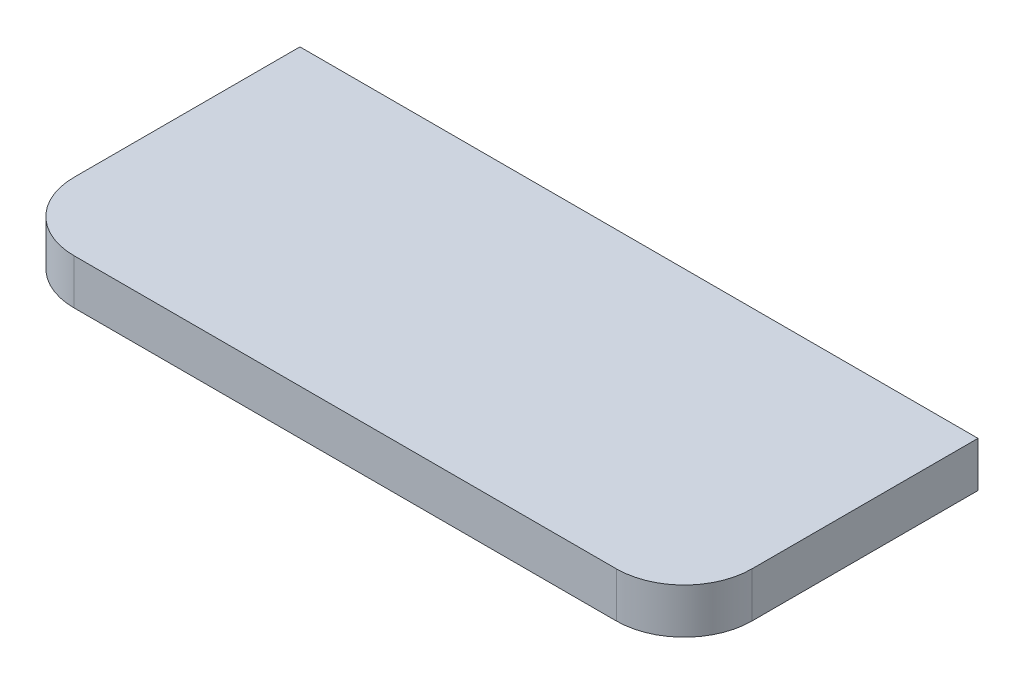
SolidWorks part; units mm, degrees
ref_plane "Front Plane" through (0, 0, 0) normal (0, 0, 1) x (1, 0, 0)
ref_plane "Top Plane" through (0, 0, 0) normal (0, 1, 0) x (1, 0, 0)
ref_plane "Right Plane" through (0, 0, 0) normal (1, 0, 0) x (0, 0, -1)
sketch "Sketch1" plane through (0, 0, 0) normal (0, 1, 0) x (1, 0, 0)
  line L0 (-75, 0) -> (75, 0)
  line L1 (75, 0) -> (75, -50)
  line L2 (-75, 0) -> (-75, -50)
  line L3 (-60, -65) -> (60, -65)
  arc A2 (-75, -50) -> (-60, -65) centre (-60, -50) ccw
  arc A3 (60, -65) -> (75, -50) centre (60, -50) ccw
  arc A4 (-60, -65) -> (-75, -50) centre (-60, -50) ccw construction
  arc A5 (75, -50) -> (60, -65) centre (60, -50) ccw construction
  point P6 (0, 0)
  point P11 (0, 0)
  point P12 (0, 0)
  dimension "D1" = 50
  dimension "D2" = 30
  dimension "D3" = 150
extrude "Boss-Extrude1" add sketch "Sketch1" along normal blind 10
